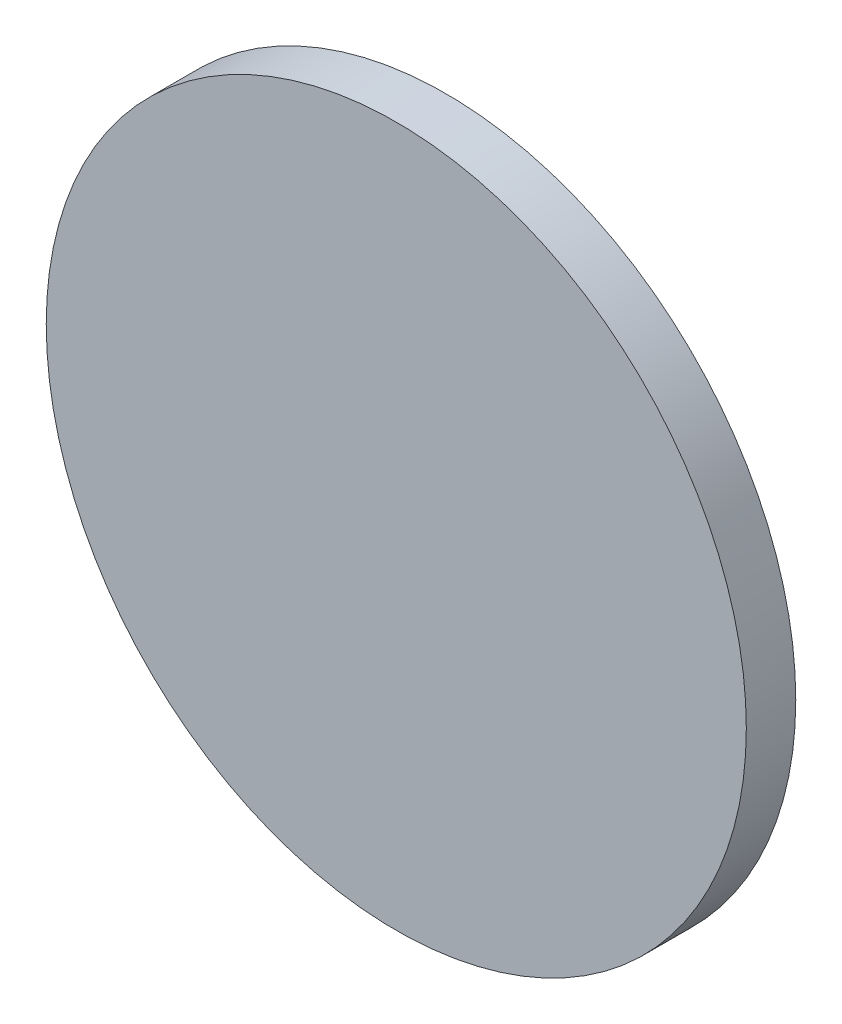
SolidWorks part; units mm, degrees
ref_plane "Front Plane" through (0, 0, 0) normal (0, 0, 1) x (1, 0, 0)
ref_plane "Top Plane" through (0, 0, 0) normal (0, 1, 0) x (1, 0, 0)
ref_plane "Right Plane" through (0, 0, 0) normal (1, 0, 0) x (0, 0, -1)
sketch "Sketch1" plane through (0, 0, 0) normal (0, 0, 1) x (1, 0, 0)
  circle A0 centre (0, 0) radius 44.958
  dimension "D1" = 89.916
extrude "Boss-Extrude1" add sketch "Sketch1" along normal blind 6.35
sketch3d "3DSketch1"
  line L0 (0, 0, 0) -> (0, 0, -158.5241) construction
